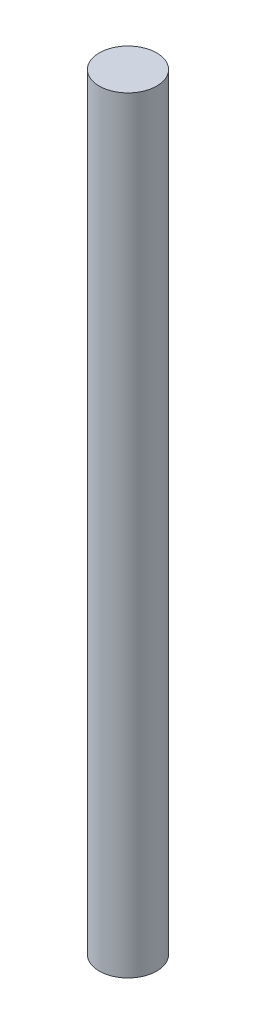
SolidWorks part; units mm, degrees
ref_plane "Front Plane" through (0, 0, 0) normal (0, 0, 1) x (1, 0, 0)
ref_plane "Top Plane" through (0, 0, 0) normal (0, 1, 0) x (1, 0, 0)
ref_plane "Right Plane" through (0, 0, 0) normal (1, 0, 0) x (0, 0, -1)
sketch "Sketch1" plane through (0, 0, 0) normal (0, 1, 0) x (1, 0, 0)
  circle A0 centre (0, 0) radius 4.7625
  dimension "D1" = 9.525
extrude "Boss-Extrude1" add sketch "Sketch1" along normal blind 127
